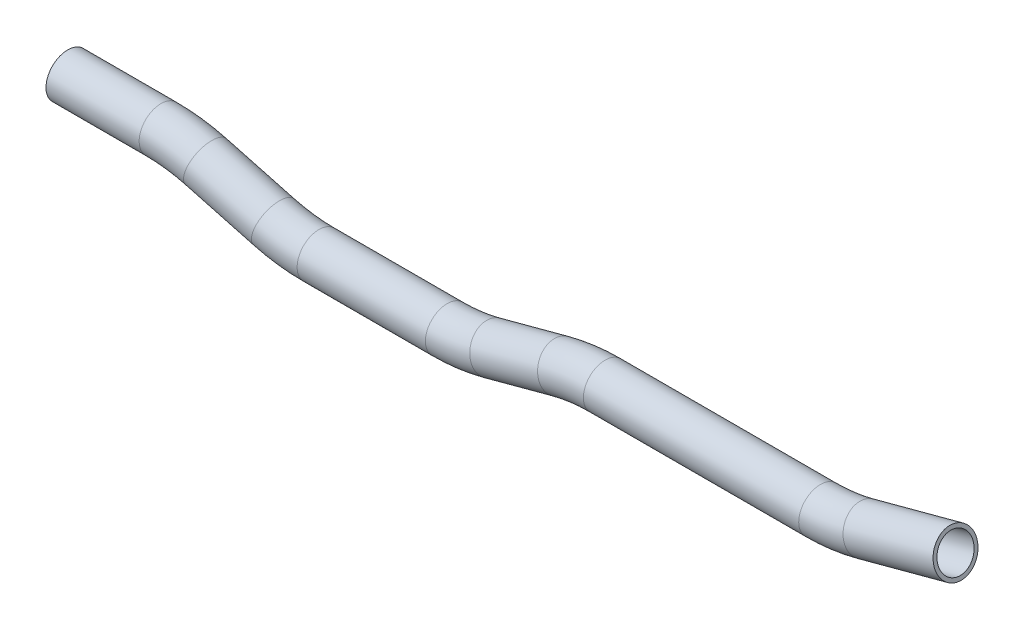
SolidWorks part; units mm, degrees
ref_plane "Front Plane" through (0, 0, 0) normal (0, 0, 1) x (1, 0, 0)
ref_plane "Top Plane" through (0, 0, 0) normal (0, 1, 0) x (1, 0, 0)
ref_plane "Right Plane" through (0, 0, 0) normal (1, 0, 0) x (0, 0, -1)
sketch "Sketch1" plane through (0, 0, 0) normal (0, 0, 1) x (1, 0, 0)
  line L0 (27.5703, 26.455) -> (68.3383, 26.455)
  line L1 (88.0604, 23.8586) -> (117.7492, 15.9035)
  line L2 (137.4712, 13.307) -> (193.6074, 13.307)
  line L3 (213.3294, 15.9035) -> (243.0182, 23.8586)
  line L4 (27.5703, 26.455) -> (116.2011, 26.455) construction
  line L5 (117.7492, 15.9035) -> (88.0604, 23.8586) construction
  line L6 (88.0604, 23.8586) -> (-12.34, 50.7608) construction
  line L7 (88.0604, 23.8586) -> (117.7492, 15.9035) construction
  line L8 (117.7492, 15.9035) -> (175.0429, 0.5517) construction
  line L9 (193.6074, 13.307) -> (137.4712, 13.307) construction
  line L10 (137.4712, 13.307) -> (51.3742, 13.307) construction
  line L11 (137.4712, 13.307) -> (193.6074, 13.307) construction
  line L12 (243.0182, 23.8586) -> (213.3294, 15.9035) construction
  line L13 (137.4712, 13.307) -> (193.6074, 13.307) construction
  line L14 (193.6074, 13.307) -> (290.4437, 13.307) construction
  line L16 (213.3294, 15.9035) -> (140.7108, -3.5546) construction
  line L17 (262.7403, 26.455) -> (356.9764, 26.455)
  line L18 (376.6984, 29.0515) -> (416.0774, 39.603)
  line L20 (213.3294, 15.9035) -> (243.0182, 23.8586) construction
  line L21 (243.0182, 23.8586) -> (336.1906, 48.824) construction
  line L22 (356.9764, 26.455) -> (262.7403, 26.455) construction
  line L23 (262.7403, 26.455) -> (179.4967, 26.455) construction
  line L24 (262.7403, 26.455) -> (356.9764, 26.455) construction
  line L25 (356.9764, 26.455) -> (448.5726, 26.455) construction
  line L27 (416.0774, 39.603) -> (376.6984, 29.0515) construction
  line L29 (376.6984, 29.0515) -> (325.2723, 15.2719) construction
  arc A0 (68.3383, 26.455) -> (88.0604, 23.8586) centre (68.3383, -49.745) cw
  arc A1 (117.7492, 15.9035) -> (137.4712, 13.307) centre (137.4712, 89.507) ccw
  arc A2 (193.6074, 13.307) -> (213.3294, 15.9035) centre (193.6074, 89.507) ccw
  arc A3 (243.0182, 23.8586) -> (262.7403, 26.455) centre (262.7403, -49.745) cw
  arc A4 (356.9764, 26.455) -> (376.6984, 29.0515) centre (356.9764, 102.655) ccw
  point P10 (203.6393, 13.307)
  point P18 (127.4393, 13.307)
  point P19 (78.3703, 26.455)
  point P25 (252.7083, 26.455)
  point P26 (367.0083, 26.455)
  point P31 (401.4602, -78.1787)
  point P33 (334.3258, -1.633)
  point P34 (0, 0)
  dimension "D3" = 76.2
  dimension "D6" = 76.2
  dimension "D9" = 76.2
  dimension "D8" = 76.2
  dimension "D10" = 76.2
  dimension "D12" = 15
  dimension "D13" = 76.2
  dimension "D1" = 50.8
  dimension "D2" = 15
  dimension "D4" = 50.8
  dimension "D5" = 15
  dimension "D7" = 15
  dimension "D11" = 15
  dimension "D14" = 50.8
  dimension "D16" = 50.8
  dimension "D17" = 114.3
ref_plane "Plane1" through (27.5703, 26.455, 0) normal (1, 0, 0) x (0, 0, -1)
sketch "Sketch2" plane through (27.5703, 26.455, 0) normal (1, 0, 0) x (0, 0, -1)
  circle A0 centre (0, 0) radius 9.525
  circle A1 centre (0, 0) radius 7.874
  dimension "D1" = 15.748
  dimension "D2" = 19.05
sweep "Sweep1" add profiles "Sketch2" path "Sketch1"
